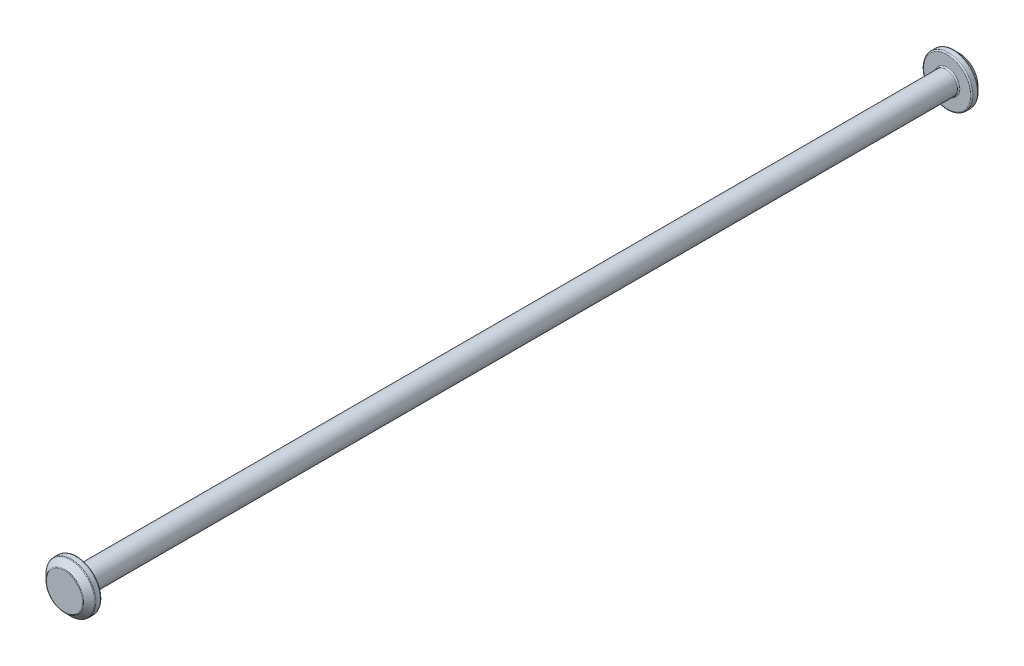
SolidWorks part; units mm, degrees
ref_plane "Front Plane" through (0, 0, 0) normal (0, 0, 1) x (1, 0, 0)
ref_plane "Top Plane" through (0, 0, 0) normal (0, 1, 0) x (1, 0, 0)
ref_plane "Right Plane" through (0, 0, 0) normal (1, 0, 0) x (0, 0, -1)
sketch "Sketch1" plane through (0, 0, 0) normal (0, 0, 1) x (1, 0, 0)
  circle A0 centre (0, 0) radius 0.925
  dimension "D1" = 1.85
extrude "Boss-Extrude1" add sketch "Sketch1" along normal blind 35.25
sketch "Sketch2" plane through (0, 0, 35.25) normal (0, 0, 1) x (1, 0, 0)
  circle A0 centre (0, 0) radius 2
  dimension "D1" = 4
extrude "Boss-Extrude2" add sketch "Sketch2" along normal blind 1
chamfer "Chamfer1" distance 0.5 angle 45 1 edges at (2, 0, 36.25)
mirror "Mirror1" about plane through (0, 0, 0) normal (0, 0, 1) of bodies 102
fillet "Fillet1" radius 0.1 8 edges at (2, 0, -35.25) (0.925, 0, -35.25) (1.5, 0, -36.25) (2, 0, -35.75) (2, 0, 35.25) (0.925, 0, 35.25) (2, 0, 35.75) (1.5, 0, 36.25)
